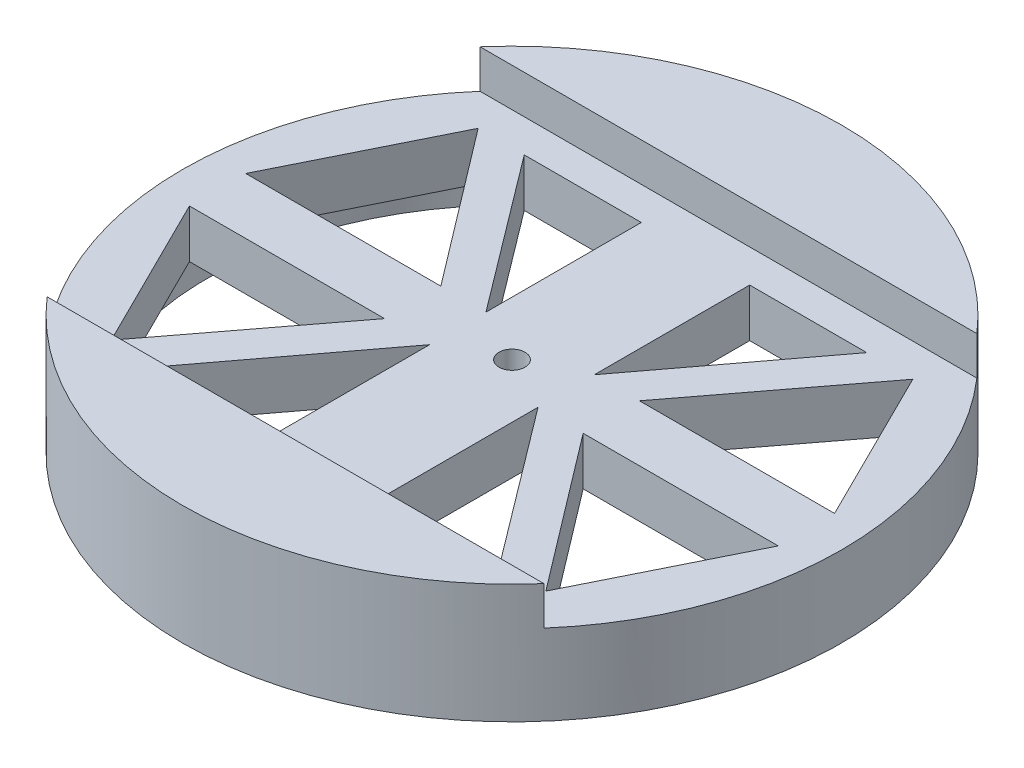
SolidWorks part; units mm, degrees
ref_plane "Front Plane" through (0, 0, 0) normal (0, 0, 1) x (1, 0, 0)
ref_plane "Top Plane" through (0, 0, 0) normal (0, 1, 0) x (1, 0, 0)
ref_plane "Right Plane" through (0, 0, 0) normal (1, 0, 0) x (0, 0, -1)
sketch "Sketch1" plane through (0, 0, 0) normal (0, 1, 0) x (1, 0, 0)
  circle A0 centre (0, 0) radius 76
  dimension "D1" = 152
extrude "Boss-Extrude1" add sketch "Sketch1" along normal blind 27.5 contours A0
sketch "Sketch2" plane through (0, 27.5, 0) normal (0, 1, 0) x (1, 0, 0)
  line L0 (-76, 0) -> (76, 0) construction
  line L1 (-58.008, 0) -> (58.008, 0) construction
  line L2 (-58.008, 49.9318) -> (58.008, 49.9318)
  line L3 (-58.008, -49.9318) -> (58.008, -49.9318)
  circle A0 centre (0, 0) radius 76 construction
  arc A1 (-58.008, 49.9318) -> (-58.008, -49.9318) centre (-58.008, 0) ccw
  arc A2 (58.008, -49.9318) -> (58.008, 49.9318) centre (58.008, 0) ccw
  point P7 (0, 0)
extrude "Cut-Extrude4" cut sketch "Sketch2" against normal blind 8.89
sketch "Sketch5" plane through (0, 18.61, 0) normal (0, 1, 0) x (1, 0, 0)
  line L0 (0, 3) -> (0, -3)
  circle A0 centre (0, 0) radius 3
extrude "Cut-Extrude5" cut sketch "Sketch5" against normal blind 20 contours A0
sketch "Sketch7" plane through (0, 18.61, 0) normal (0, 1, 0) x (1, 0, 0)
  line L0 (-50.1251, 42.3228) -> (-67.9029, 6.4906)
  line L1 (-67.9029, 6.4906) -> (-22.9029, 6.4906)
  line L2 (-22.9029, 6.4906) -> (-50.1251, 42.3228)
  line L3 (0, 49.9318) -> (0, -49.9318) construction
  line L4 (57.2959, 49.9318) -> (-57.2959, 49.9318) construction
  line L5 (-57.2959, -49.9318) -> (57.2959, -49.9318) construction
  line L6 (67.9029, 6.4906) -> (22.9029, 6.4906)
  line L7 (50.1251, 42.3228) -> (67.9029, 6.4906)
  line L8 (22.9029, 6.4906) -> (50.1251, 42.3228)
  line L9 (-76, 0) -> (76, 0) construction
  line L10 (50.1251, -42.3228) -> (67.9029, -6.4906)
  line L11 (22.9029, -6.4906) -> (50.1251, -42.3228)
  line L12 (67.9029, -6.4906) -> (22.9029, -6.4906)
  line L13 (-67.9029, -6.4906) -> (-22.9029, -6.4906)
  line L14 (-50.1251, -42.3228) -> (-67.9029, -6.4906)
  line L15 (-22.9029, -6.4906) -> (-50.1251, -42.3228)
  arc A0 (-57.2959, 49.9318) -> (-57.2959, -49.9318) centre (0, 0) ccw construction
  arc A1 (57.2959, -49.9318) -> (57.2959, 49.9318) centre (0, 0) ccw construction
  dimension "D1" = 40
  dimension "D2" = 45
  dimension "D3" = 45
extrude "Cut-Extrude6" cut sketch "Sketch7" against normal through all
sketch "Sketch9" plane through (0, 18.61, 0) normal (0, 1, 0) x (1, 0, 0)
  line L0 (-12.5, 6.4906) -> (-12.5, 42.3228)
  line L1 (-12.5, 42.3228) -> (-39.5, 42.3228)
  line L2 (-12.5, 6.4906) -> (-39.5, 42.3228)
  line L3 (0, 49.9318) -> (0, -49.9318) construction
  line L4 (57.2959, 49.9318) -> (-57.2959, 49.9318) construction
  line L5 (-57.2959, -49.9318) -> (57.2959, -49.9318) construction
  line L6 (-76, 0) -> (76, 0) construction
  line L7 (12.5, 6.4906) -> (39.5, 42.3228)
  line L8 (12.5, 42.3228) -> (39.5, 42.3228)
  line L9 (12.5, 6.4906) -> (12.5, 42.3228)
  line L10 (12.5, -6.4906) -> (12.5, -42.3228)
  line L11 (12.5, -42.3228) -> (39.5, -42.3228)
  line L12 (12.5, -6.4906) -> (39.5, -42.3228)
  line L13 (-12.5, -6.4906) -> (-39.5, -42.3228)
  line L14 (-12.5, -42.3228) -> (-39.5, -42.3228)
  line L15 (-12.5, -6.4906) -> (-12.5, -42.3228)
  arc A0 (-57.2959, 49.9318) -> (-57.2959, -49.9318) centre (0, 0) ccw construction
  arc A1 (57.2959, -49.9318) -> (57.2959, 49.9318) centre (0, 0) ccw construction
  dimension "D1" = 27
  dimension "D2" = 12.5
  dimension "D3" = 27
extrude "Cut-Extrude7" cut sketch "Sketch9" against normal through all
sketch "Sketch10" plane through (0, 18.61, 0) normal (0, 1, 0) x (1, 0, 0)
  line L0 (-22.9029, 6.4906) -> (-50.1251, 42.3228) construction
  line L1 (-39.5, 42.3228) -> (-12.5, 6.4906) construction
  dimension "D1" = 16.5359
sketch "Sketch11" plane through (0, 0, 0) normal (0, -1, 0) x (1, 0, 0)
sketch "Sketch13" plane through (0, 0, 0) normal (0, -1, 0) x (-1, 0, 0)
  circle A0 centre (0, 0) radius 70
  dimension "D1" = 140
extrude "Cut-Extrude9" cut sketch "Sketch13" against normal blind 7.5
